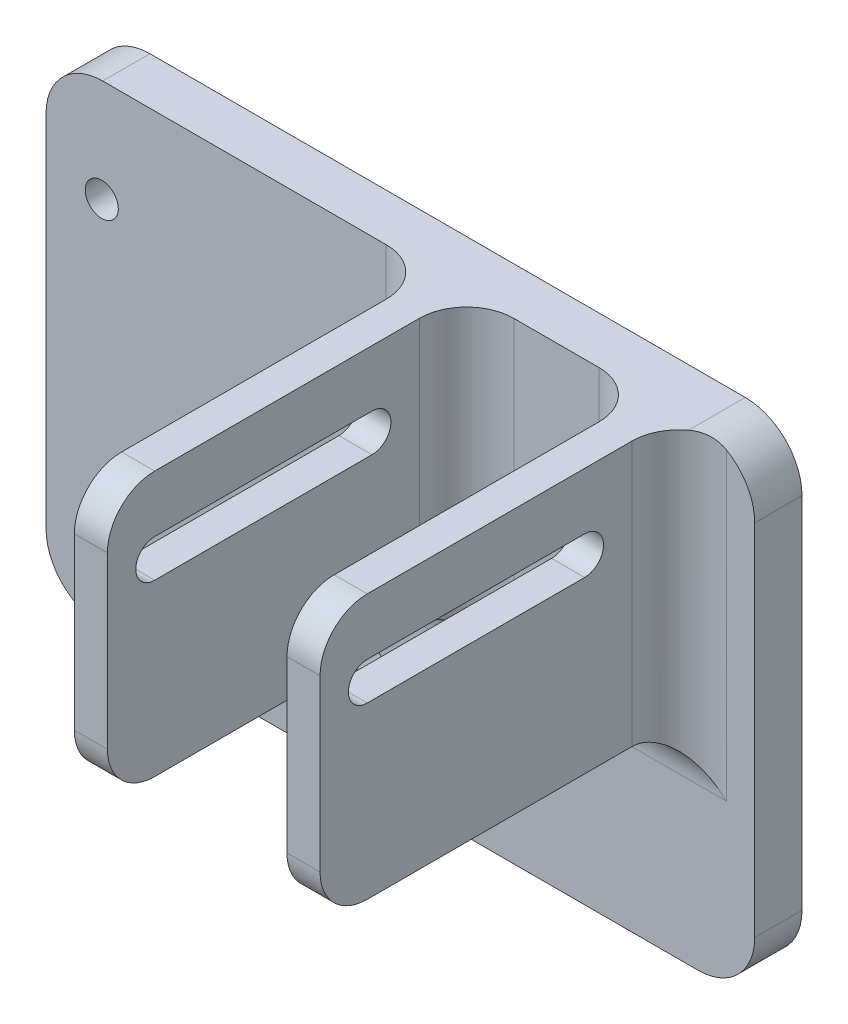
SolidWorks part; units mm, degrees
ref_plane "前视基准面" through (0, 0, 0) normal (0, 0, 1) x (1, 0, 0)
ref_plane "上视基准面" through (0, 0, 0) normal (0, 1, 0) x (1, 0, 0)
ref_plane "右视基准面" through (0, 0, 0) normal (1, 0, 0) x (0, 0, -1)
sketch "Sketch1" plane through (0, 0, 0) normal (0, 0, 1) x (1, 0, 0)
  line L1 (-13, -14) -> (13, -14)
  line L2 (-13, -14) -> (-13, 14)
  line L3 (-13, 14) -> (13, 14)
  line L4 (13, -14) -> (13, 14)
  line L5 (-13, -14) -> (13, 14) construction
  line L6 (-13, 14) -> (13, -14) construction
  line L7 (-9.5, -14) -> (9.5, -14)
  line L8 (-9.5, -14) -> (-9.5, 14)
  line L9 (-9.5, 14) -> (9.5, 14)
  line L10 (9.5, -14) -> (9.5, 14)
  line L11 (-9.5, -14) -> (9.5, 14) construction
  line L12 (-9.5, 14) -> (9.5, -14) construction
  point P0 (0, 0)
  point P6 (0, 0)
  dimension "D1" = 19
  dimension "D2" = 3.5
  dimension "D3" = 28
extrude "Boss-Extrude1" add sketch "Sketch1" along normal blind 38 contours L1 L8 L3 L2 | L10 L1 L4 L3
sketch "Sketch2" plane through (0, 0, 0) normal (0, 0, -1) x (-1, 0, 0)
  line L4 (-21, 14) -> (-21, -36)
  line L5 (-21, 14) -> (54, 14)
  line L6 (-21, -36) -> (54, -36)
  line L7 (54, 14) -> (54, -36)
  line L9 (-13, -14) -> (-13, 14) construction
  line L10 (-9.5, 14) -> (-13, 14) construction
  dimension "D1" = 50
  dimension "D2" = 8
  dimension "D3" = 75
extrude "Boss-Extrude2" add sketch "Sketch2" along normal blind 5
fillet "Fillet1" radius 6 4 edges at (-54, -36, -2.5) (-54, 14, -2.5) (21, 14, -2.5) (21, -36, -2.5)
fillet "Fillet2" radius 5 10 edges at (11.25, -14, 38) (11.25, 14, 38) (-11.25, 14, 38) (-11.25, -14, 38) (-11.25, -14, 0) (11.25, -14, 0) (-13, 0, 0) (13, 0, 0) (-9.5, 0, 0) (9.5, 0, 0)
sketch "Sketch3" plane through (13, 0, 0) normal (1, 0, 0) x (0, 0, -1)
  line L0 (-38, -9) -> (-38, 9) construction
  line L1 (-33, 14) -> (-5, 14) construction
  line L2 (-10, 6) -> (-33, 6) construction
  line L3 (-10, 4) -> (-33, 4)
  line L4 (-10, 8) -> (-33, 8)
  line L5 (-5, -14) -> (-5, 14) construction
  circle A0 centre (-26, 6) radius 2
  arc A1 (-10, 4) -> (-10, 8) centre (-10, 6) ccw
  arc A2 (-33, 8) -> (-33, 4) centre (-33, 6) ccw
  point P8 (-21.5, 6)
  point P13 (0, 0)
  dimension "D1" = 12
  dimension "D2" = 8
  dimension "D3" = 4
  dimension "D4" = 5
  dimension "D5" = 5
extrude "Cut-Extrude1" cut sketch "Sketch3" against normal through all both and the other way through all
sketch "Sketch4" plane through (0, 0, -5) normal (0, 0, -1) x (-1, 0, 0)
  line L0 (54, -11) -> (34, -11) construction
  line L1 (48.1, -25.1) -> (19.9, -25.1) construction
  line L2 (48.1, -25.1) -> (48.1, 3.1) construction
  line L3 (48.1, 3.1) -> (19.9, 3.1) construction
  line L4 (19.9, -25.1) -> (19.9, 3.1) construction
  line L5 (48.1, -25.1) -> (19.9, 3.1) construction
  line L6 (48.1, 3.1) -> (19.9, -25.1) construction
  line L7 (54, -30) -> (54, 8) construction
  circle A0 centre (19.9, 3.1) radius 1.75
  circle A1 centre (48.1, 3.1) radius 1.75
  circle A2 centre (48.1, -25.1) radius 1.75
  circle A3 centre (19.9, -25.1) radius 1.75
  point P0 (34, -11)
  dimension "D1" = 3.5
  dimension "D2" = 28.2
  dimension "D3" = 20
extrude "Cut-Extrude2" cut sketch "Sketch4" against normal through all both and the other way through all
